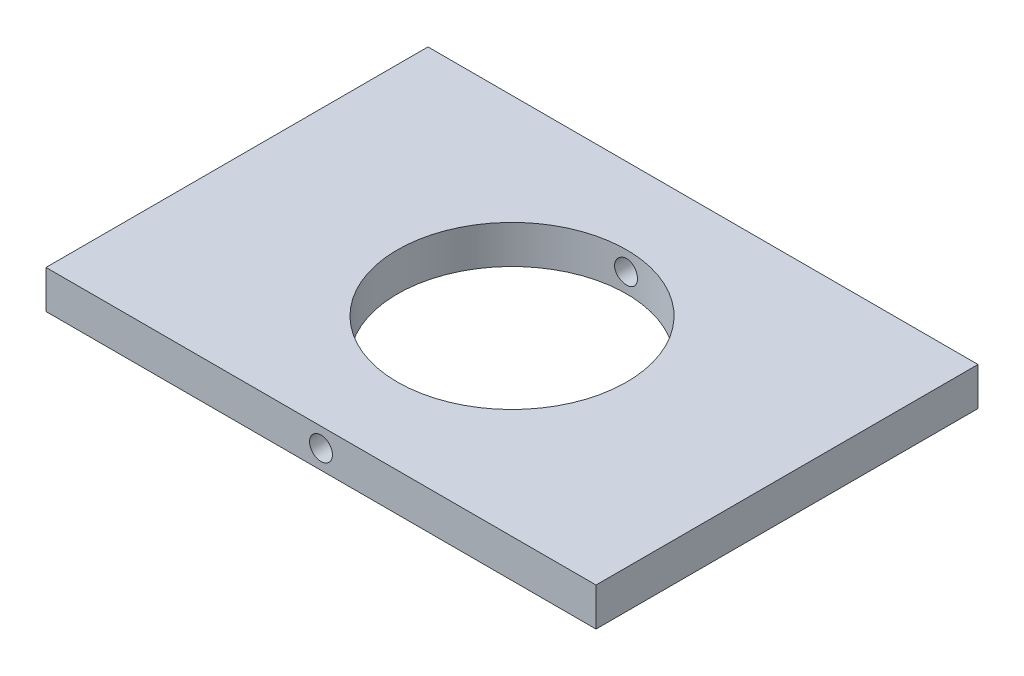
SolidWorks part; units mm, degrees
ref_plane "Plan de face" through (0, 0, 0) normal (0, 0, 1) x (1, 0, 0)
ref_plane "Plan de dessus" through (0, 0, 0) normal (0, 1, 0) x (1, 0, 0)
ref_plane "Plan de droite" through (0, 0, 0) normal (1, 0, 0) x (0, 0, -1)
sketch "Esquisse1" plane through (0, 0, 0) normal (0, 0, 1) x (1, 0, 0)
  line L0 (-19.5, -47.5) -> (52.5, -47.5) construction
  line L5 (-19.5, -45) -> (52.5, -45)
  line L6 (-19.5, -45) -> (-19.5, -50)
  line L7 (-19.5, -50) -> (52.5, -50)
  line L8 (52.5, -45) -> (52.5, -50)
  line L9 (16.5, -45) -> (16.5, -50) construction
  dimension "D1" = 5
  dimension "D2" = 72
extrude "Boss.-Extru.1" add sketch "Esquisse1" along normal blind 50
sketch "Esquisse2" plane through (0, -45, 0) normal (0, 1, 0) x (-1, 0, 0)
  line L0 (19.5, 50) -> (-52.5, 50) construction
  line L7 (-52.5, 50) -> (-52.5, 0) construction
  circle A0 centre (-16.5, 25) radius 15
  dimension "D10" = 36
  dimension "D11" = 25
extrude "Enlèv. mat.-Extru.1" cut sketch "Esquisse2" against normal through all
sketch "Esquisse5" plane through (0, 0, 50) normal (0, 0, 1) x (1, 0, 0)
  line L0 (-19.5, -45) -> (52.5, -45) construction
  line L1 (-19.5, -45) -> (-19.5, -50) construction
  circle A0 centre (16.5, -47.5) radius 1.5
  dimension "D1" = 2.5
  dimension "D2" = 36
extrude "Enlèv. mat.-Extru.4" cut sketch "Esquisse5" against normal through all
